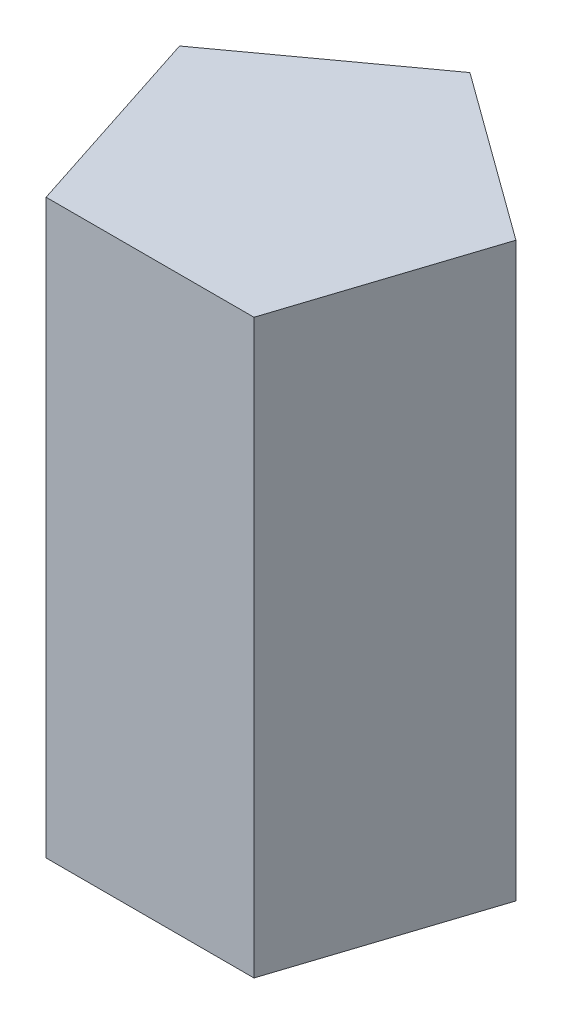
SolidWorks part; units mm, degrees
ref_plane "Front" through (0, 0, 0) normal (0, 0, 1) x (1, 0, 0)
ref_plane "Top" through (0, 0, 0) normal (0, 1, 0) x (1, 0, 0)
ref_plane "Right" through (0, 0, 0) normal (1, 0, 0) x (0, 0, -1)
sketch "Sketch1" plane through (0, 0, 0) normal (0, 1, 0) x (1, 0, 0)
  line L1 (5.8779, 1.9098) -> (0, 6.1803)
  line L2 (0, 6.1803) -> (-5.8779, 1.9098)
  line L3 (-5.8779, 1.9098) -> (-3.6327, -5)
  line L4 (-3.6327, -5) -> (3.6327, -5)
  line L5 (3.6327, -5) -> (5.8779, 1.9098)
  circle A0 centre (0, 0) radius 5 construction
  dimension "D1" = 10
extrude "Extrude1" add sketch "Sketch1" along normal blind 20
